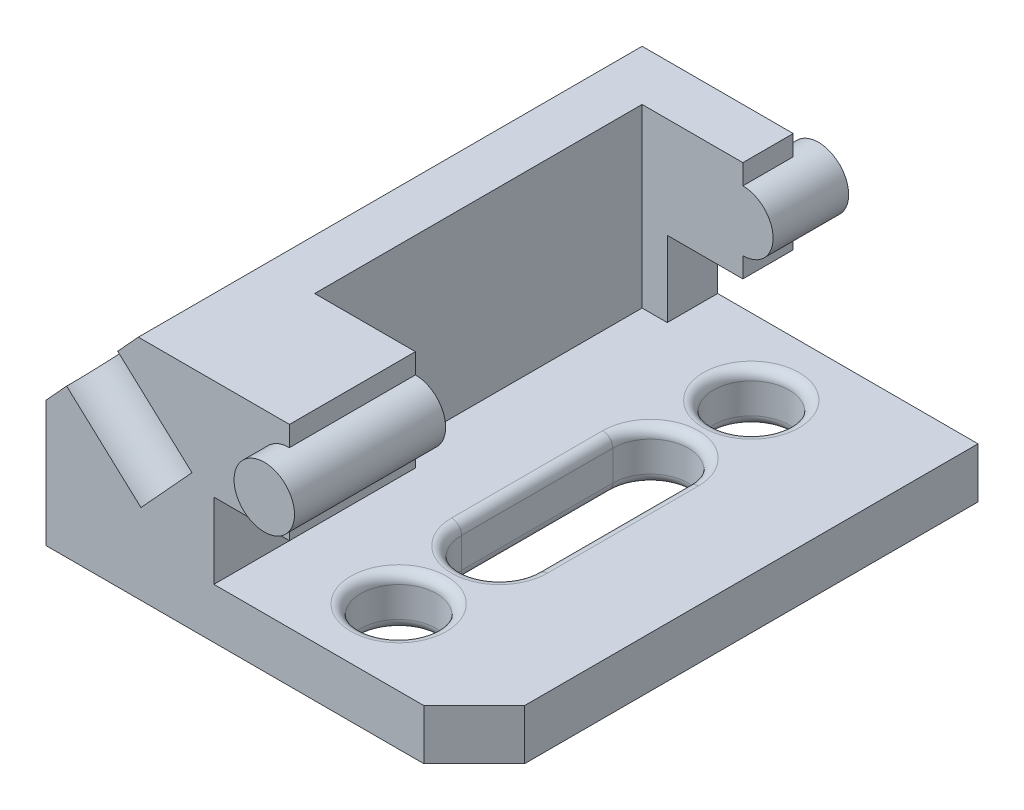
SolidWorks part; units mm, degrees
material "1060 Alloy"
ref_plane "Front Plane" through (0, 0, 0) normal (0, 0, 1) x (1, 0, 0)
ref_plane "Top Plane" through (0, 0, 0) normal (0, 1, 0) x (1, 0, 0)
ref_plane "Right Plane" through (0, 0, 0) normal (1, 0, 0) x (0, 0, -1)
sketch "Sketch1" plane through (0, 0, 0) normal (0, 0, 1) x (1, 0, 0)
  line L0 (0, 0) -> (0, 25)
  line L1 (0, 0) -> (85, 0)
  line L2 (85, 0) -> (85, 10)
  line L3 (85, 10) -> (33.3266, 10)
  line L4 (33.3266, 10) -> (33.3266, 25)
  line L5 (33.3266, 25) -> (48.3266, 25)
  line L6 (48.3266, 25) -> (48.3266, 45)
  line L7 (48.3266, 45) -> (18.3266, 45)
  line L9 (18.3266, 45) -> (0, 25)
  circle A0 centre (48.3266, 35) radius 6
  dimension "D10" = 12
  dimension "D1" = 25
  dimension "D2" = 85
  dimension "D3" = 10
  dimension "D4" = 15
  dimension "D5" = 15
  dimension "D6" = 20
  dimension "D7" = 30
  dimension "D8" = 42.5
  dimension "D9" = 10
extrude "Boss-Extrude1" add sketch "Sketch1" along normal blind 100 contours A0 L6 L7 L9 L0 L1 L2 L3 L4 L5 | L6 A0 | L6 A0
sketch "Sketch3" plane through (0, 0, 100) normal (0, 0, 1) x (1, 0, 0)
  circle A0 centre (48.3266, 35) radius 6
  arc A1 (48.3266, 29) -> (48.3266, 41) centre (48.3266, 35) ccw construction
extrude "Boss-Extrude2" add sketch "Sketch3" along normal blind 5
sketch "Sketch4" plane through (0, 0, 0) normal (0, 0, -1) x (-1, 0, 0)
  circle A0 centre (-48.3266, 35) radius 6
  arc A1 (-48.3266, 41) -> (-48.3266, 29) centre (-48.3266, 35) ccw construction
extrude "Boss-Extrude3" add sketch "Sketch4" along normal blind 5
sketch "Sketch5" plane through (-12.4524, 11.4106, 0) normal (-0.7373, 0.6756, 0) x (0.6756, 0.7373, 0)
  line L0 (31.9954, 0) -> (31.9954, -100) construction
  line L1 (45.5588, 0) -> (18.4319, 0) construction
  line L2 (45.5588, -100) -> (18.4319, -100) construction
  circle A0 centre (31.9954, -100) radius 7.5
  dimension "D1" = 15
extrude "Cut-Extrude1" cut sketch "Sketch5" against normal blind 20
sketch "Sketch6" plane through (0, 45, 0) normal (0, 1, 0) x (1, 0, 0)
  line L0 (48.3266, 0) -> (48.3266, -10) construction
  line L1 (48.3266, -100) -> (48.3266, 0) construction
  line L2 (48.3266, -10) -> (28.3266, -10)
  line L3 (18.3266, -100) -> (18.3266, 0) construction
  line L4 (28.3266, -10) -> (28.3266, -75)
  line L5 (28.3266, -75) -> (54.3266, -75)
  line L6 (54.3266, -105) -> (54.3266, 5) construction
  line L7 (54.3266, -75) -> (54.3266, -10)
  line L8 (48.3266, -10) -> (54.3266, -10)
  point P8 (0, 0)
  dimension "D1" = 10
  dimension "D2" = 10
  dimension "D3" = 65
extrude "Cut-Extrude2" cut sketch "Sketch6" against normal up to surface (35 mm away) up to face at (59.1633, 10, 50)
sketch "Sketch8" plane through (0, 10, 0) normal (0, 1, 0) x (1, 0, 0)
  line L0 (85, -100) -> (85, 0) construction
  line L1 (85, 0) -> (33.3266, 0) construction
  line L2 (85, -50) -> (28.3266, -50) construction
  line L3 (28.3266, -10) -> (28.3266, -75) construction
  line L4 (47.5, -15) -> (47.5, -50) construction
  line L5 (62.5, -15) -> (62.5, -50) construction
  line L6 (47.5, -65) -> (47.5, -35)
  line L7 (62.5, -65) -> (62.5, -35)
  circle A0 centre (55, -15) radius 7.5
  arc A1 (47.5, -35) -> (62.5, -35) centre (55, -35) cw
  circle A2 centre (55, -85) radius 7.5
  arc A3 (47.5, -65) -> (62.5, -65) centre (55, -65) ccw
  dimension "D1" = 15
  dimension "D2" = 30
  dimension "D3" = 15
  dimension "D4" = 15
extrude "Cut-Extrude3" cut sketch "Sketch8" against normal up to surface (10 mm away) up to face at (42.5, 0, 50)
sketch "Sketch9" plane through (0, 10, 0) normal (0, 1, 0) x (1, 0, 0)
  line L0 (75, -100) -> (85, -90)
  line L1 (85, -100) -> (33.3266, -100) construction
  line L2 (85, -100) -> (85, 0) construction
  line L3 (75, -100) -> (85, -100)
  line L4 (85, -100) -> (85, -90)
  dimension "D1" = 10
  dimension "D2" = 45
extrude "Cut-Extrude4" cut sketch "Sketch9" against normal up to surface (10 mm away) up to face at (55, 0, 22.5)
fillet "Fillet1" radius 2 12 edges at (55, 0, 72.5) (62.5, 0, 50) (55, 0, 27.5) (62.5, 10, 50) (55, 10, 72.5) (47.5, 10, 50) (55, 0, 22.5) (47.5, 0, 50) (55, 0, 92.5) (62.5, 10, 85) (55, 10, 27.5) (47.5, 10, 15)
equation "\"A\" = 85"
equation "\"B\" = 65"
equation "\"C\"= 42.50deg"
equation "\"D2@Sketch1\"=\"A\""
equation "\"D8@Sketch1\"=\"C\""
equation "\"D3@Sketch6\"=\"B\""
